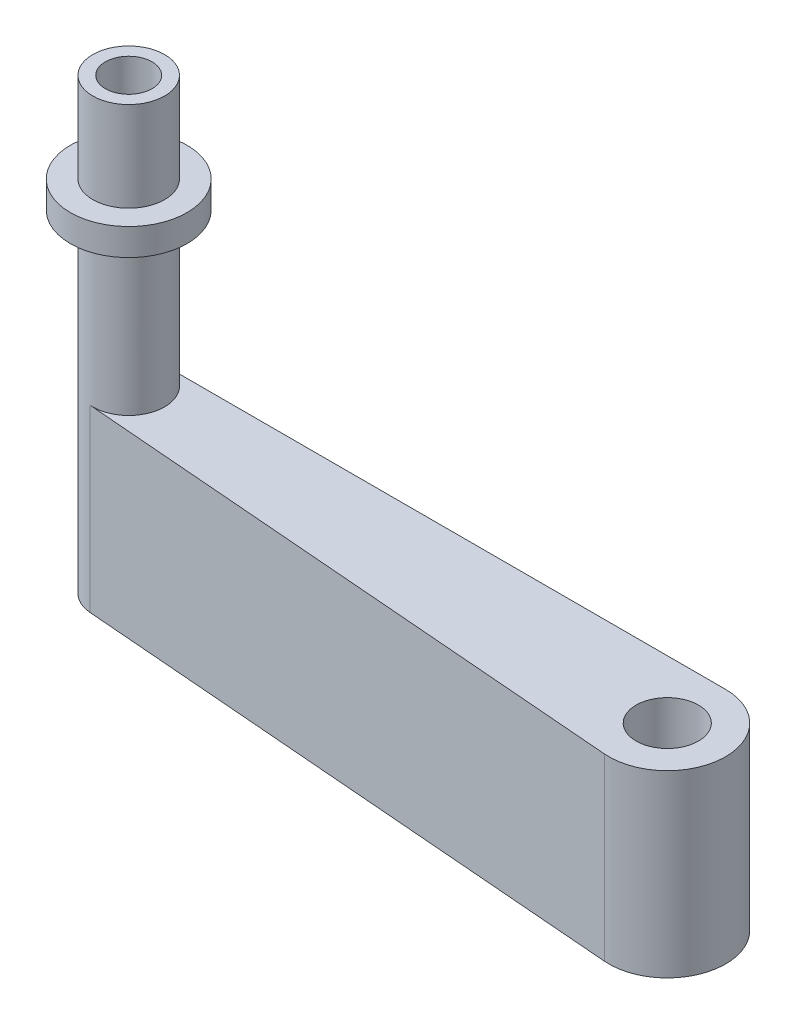
SolidWorks part; units mm, degrees
ref_plane "Alzado" through (0, 0, 0) normal (0, 0, 1) x (1, 0, 0)
ref_plane "Planta" through (0, 0, 0) normal (0, 1, 0) x (1, 0, 0)
ref_plane "Vista lateral" through (0, 0, 0) normal (1, 0, 0) x (0, 0, -1)
sketch "Croquis1" plane through (0, 0, 0) normal (0, 1, 0) x (1, 0, 0)
  line L0 (-62.5, 6.5) -> (0, 6.5)
  line L2 (0, 15.0922) -> (0, -13.2624) construction
  line L3 (70.9164, 0) -> (-21.8302, 0) construction
  line L4 (-62.8195, -1.4872) -> (-0.5192, -6.4792)
  arc A0 (-62.5, 6.5) -> (-62.8195, -1.4872) centre (-62.5, 2.5) ccw
  arc A2 (-0.5192, -6.4792) -> (0, 6.5) centre (0, 0) ccw
  dimension "D1" = 13
  dimension "D2" = 4
  dimension "D4" = 73
extrude "Saliente-Extruir1" add sketch "Croquis1" along normal mid plane 20
sketch "Croquis2" plane through (0, 10, 0) normal (0, 1, 0) x (1, 0, 0)
  circle A0 centre (0, 0) radius 3.475
  dimension "D1" = 6.95
extrude "Cortar-Extruir1" cut sketch "Croquis2" against normal through all
sketch "Croquis3" plane through (0, 10, 0) normal (0, 1, 0) x (1, 0, 0)
  circle A0 centre (-62.5, 2.5) radius 4
  arc A1 (-62.5, 6.5) -> (-62.8195, -1.4872) centre (-62.5, 2.5) ccw construction
extrude "Saliente-Extruir2" add sketch "Croquis3" along normal blind 30
sketch "Croquis4" plane through (0, 40, 0) normal (0, 1, 0) x (1, 0, 0)
  circle A0 centre (-62.5, 2.5) radius 2.6
  dimension "D1" = 5.2
extrude "Cortar-Extruir2" cut sketch "Croquis4" against normal blind 10 contours A0
sketch "Croquis6" plane through (0, 40, 0) normal (0, 1, 0) x (1, 0, 0)
  circle A0 centre (-62.5, 2.5) radius 4
  circle A1 centre (-62.5, 2.5) radius 6.5
  dimension "D1" = 8
  dimension "D2" = 2.5
extrude "Saliente-Extruir3" add sketch "Croquis6" along normal blind 3 from offset 13 separate body
